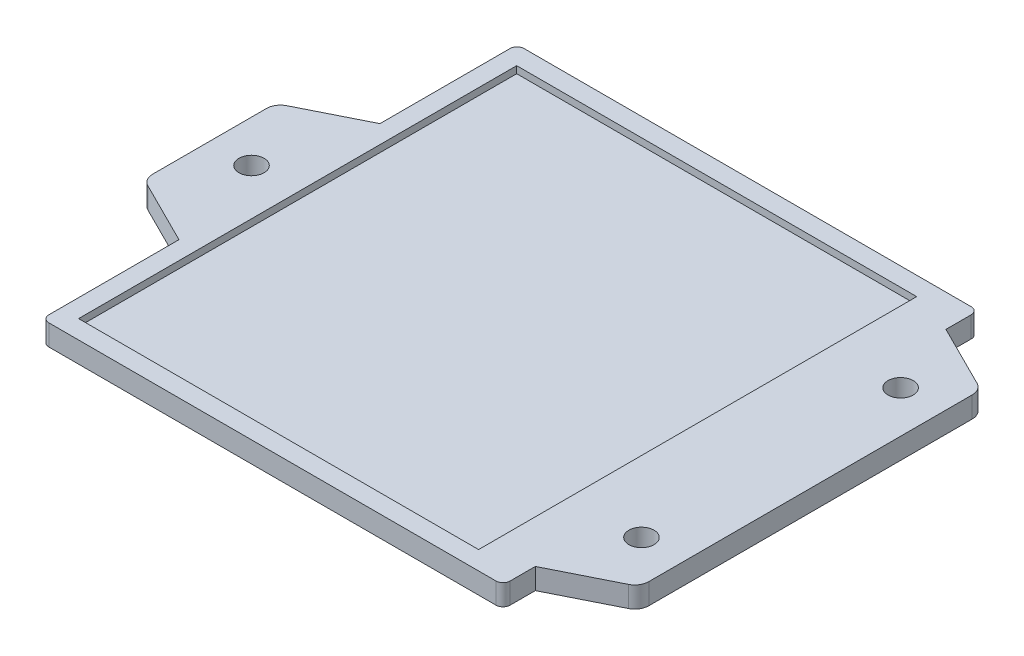
SolidWorks part; units mm, degrees
ref_plane "Front Plane" through (0, 0, 0) normal (0, 0, 1) x (1, 0, 0)
ref_plane "Top Plane" through (0, 0, 0) normal (0, 1, 0) x (1, 0, 0)
ref_plane "Right Plane" through (0, 0, 0) normal (1, 0, 0) x (0, 0, -1)
sketch "Sketch1" plane through (0, 0, 0) normal (0, 1, 0) x (-1, 0, 0)
  line L0 (-33, 29.382) -> (-33, 33)
  line L1 (-32, 34) -> (32, 34)
  line L2 (33, 33) -> (33, 14.382)
  line L3 (33, 14.382) -> (41.8944, 9.9348)
  line L4 (43, 8.1459) -> (43, -8.1459)
  line L5 (41.8944, -9.9348) -> (33, -14.382)
  line L6 (33, -14.382) -> (33, -33)
  line L7 (32, -34) -> (-32, -34)
  line L8 (-33, -33) -> (-33, -29.382)
  line L9 (-33, -29.382) -> (-41.8944, -24.9348)
  line L10 (-43, -23.1459) -> (-43, 23.1459)
  line L11 (-41.8944, 24.9348) -> (-33, 29.382)
  arc A1 (-41.8944, -24.9348) -> (-43, -23.1459) centre (-41, -23.1459) cw
  arc A2 (-43, 23.1459) -> (-41.8944, 24.9348) centre (-41, 23.1459) cw
  arc A3 (41.8944, 9.9348) -> (43, 8.1459) centre (41, 8.1459) cw
  arc A4 (43, -8.1459) -> (41.8944, -9.9348) centre (41, -8.1459) cw
  arc A5 (-32, -34) -> (-33, -33) centre (-32, -33) cw
  arc A6 (33, -33) -> (32, -34) centre (32, -33) cw
  arc A7 (32, 34) -> (33, 33) centre (32, 33) cw
  arc A8 (-33, 33) -> (-32, 34) centre (-32, 33) cw
  circle A9 centre (-37, 18.1929) radius 1.8
  circle A10 centre (-37, -18.8964) radius 1.8
  circle A11 centre (37, 0) radius 1.8
  point P25 (-43, -24.382)
  point P30 (-43, 24.382)
  point P55 (37.0737, 0)
  dimension "D1" = 2
  dimension "D2" = 1
extrude "Boss-Extrude1" add sketch "Sketch1" along normal blind 3
sketch "Sketch3" plane through (0, 0, 0) normal (0, 1, 0) x (-1, 0, 0)
  line L13 (-26.85, -31.35) -> (30.4, -31.35)
  line L14 (-26.85, -31.35) -> (-26.85, 31.35)
  line L15 (-26.85, 31.35) -> (30.4, 31.35)
  line L16 (30.4, -31.35) -> (30.4, 31.35)
  point P55 (37.0737, 0)
extrude "Cut-Extrude1" cut sketch "Sketch3" against normal blind 1 from surface at 3 starting at face at (0, 3, 0)
